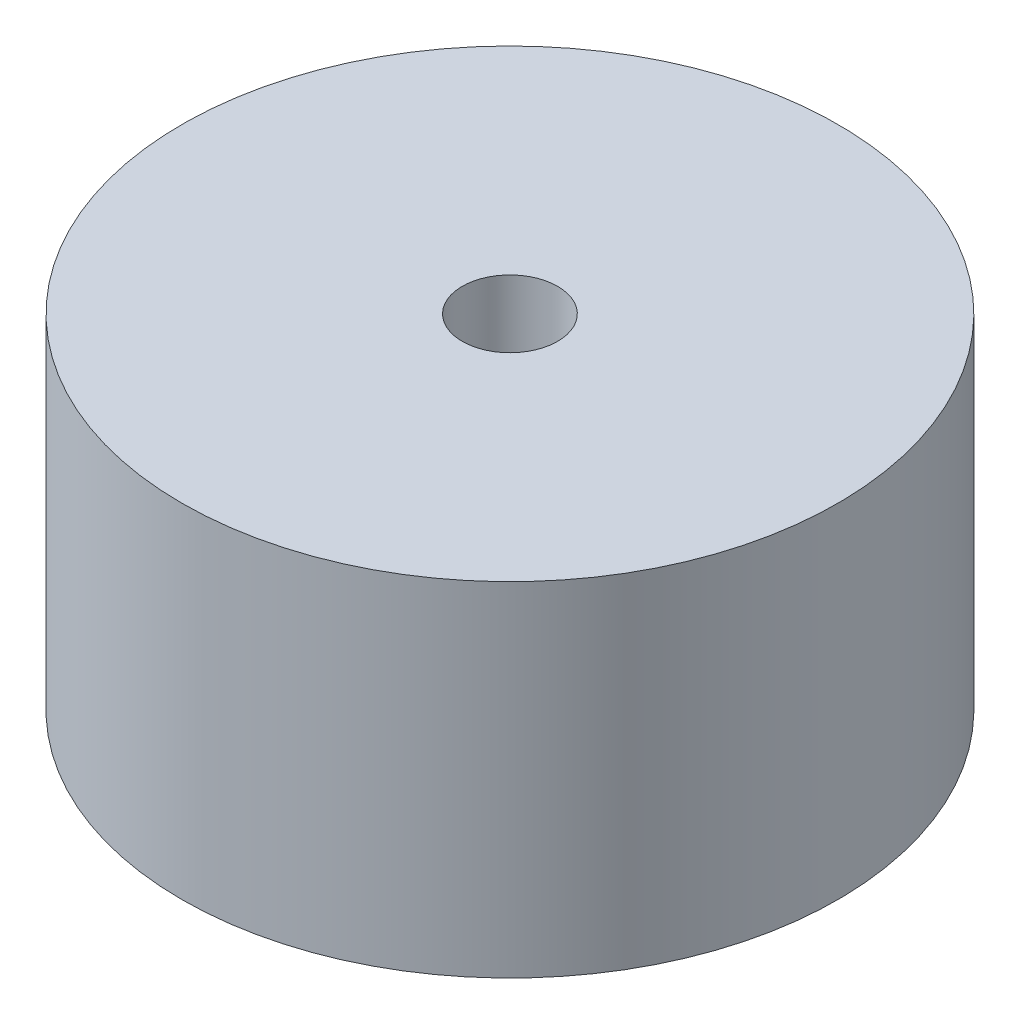
SolidWorks part; units mm, degrees
material "Aluminum Bronze"
ref_plane "Front Plane" through (0, 0, 0) normal (0, 0, 1) x (1, 0, 0)
ref_plane "Top Plane" through (0, 0, 0) normal (0, 1, 0) x (1, 0, 0)
ref_plane "Right Plane" through (0, 0, 0) normal (1, 0, 0) x (0, 0, -1)
sketch "Sketch1" plane through (0, 0, 0) normal (0, 1, 0) x (1, 0, 0)
  circle A0 centre (0, 0) radius 34.4
  dimension "D1" = 68.8
extrude "Boss-Extrude1" add sketch "Sketch1" along normal blind 36
sketch "Sketch2" plane through (0, 0, 0) normal (0, -1, 0) x (1, 0, 0)
  circle A0 centre (0, 0) radius 5
  dimension "D1" = 10
extrude "Cut-Extrude1" cut sketch "Sketch2" against normal blind 36
